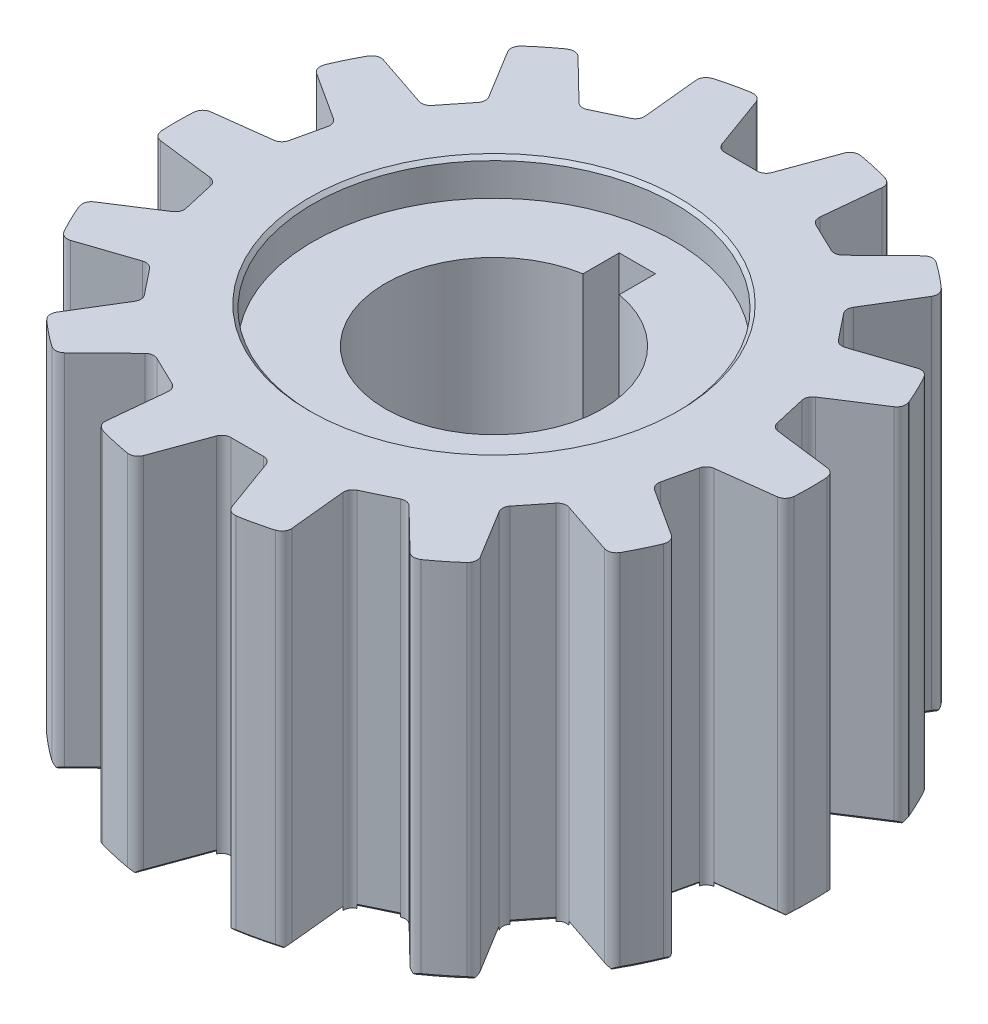
SolidWorks part; units mm, degrees
ref_plane "Alzado" through (0, 0, 0) normal (0, 0, 1) x (1, 0, 0)
ref_plane "Planta" through (0, 0, 0) normal (0, 1, 0) x (1, 0, 0)
ref_plane "Vista lateral" through (0, 0, 0) normal (1, 0, 0) x (0, 0, -1)
sketch "Croquis1" plane through (0, 0, 0) normal (0, 1, 0) x (1, 0, 0)
  circle A5 centre (0, 0) radius 6
  circle A8 centre (0, 0) radius 17.5
  dimension "D1" = 12
  dimension "D2" = 35
extrude "Saliente-Extruir1" add sketch "Croquis1" along normal blind 20
sketch "Croquis2" plane through (0, 20, 0) normal (0, 1, 0) x (1, 0, 0)
  line L0 (5.916, 12.2847) -> (7.0422, 11.7423)
  line L1 (7.0422, 11.7423) -> (9.8402, 14.4714)
  line L2 (0, 13.635) -> (-1.25, 13.635)
  line L3 (0, 13.635) -> (1.25, 13.635)
  line L4 (1.25, 13.635) -> (2.5868, 17.3078)
  line L6 (-2.5868, 17.3078) -> (-1.25, 13.635)
  line L7 (5.1789, 16.7161) -> (4.7898, 12.8271)
  line L8 (5.916, 12.2847) -> (4.7898, 12.8271)
  line L9 (10.6603, 8.5013) -> (11.4396, 7.524)
  line L10 (11.4396, 7.524) -> (15.1446, 8.7688)
  line L11 (11.9189, 12.8136) -> (9.8809, 9.4786)
  line L12 (10.6603, 8.5013) -> (9.8809, 9.4786)
  line L13 (13.2931, 3.0341) -> (13.5713, 1.8154)
  line L14 (13.5713, 1.8154) -> (17.4494, 1.3294)
  line L15 (16.2982, 6.3733) -> (13.015, 4.2527)
  line L16 (13.2931, 3.0341) -> (13.015, 4.2527)
  line L17 (13.2931, -3.0341) -> (13.015, -4.2527)
  line L18 (13.015, -4.2527) -> (16.2982, -6.3733)
  line L19 (17.4494, -1.3294) -> (13.5713, -1.8154)
  line L20 (13.2931, -3.0341) -> (13.5713, -1.8154)
  line L21 (10.6603, -8.5013) -> (9.8809, -9.4786)
  line L22 (9.8809, -9.4786) -> (11.9189, -12.8136)
  line L23 (15.1446, -8.7688) -> (11.4396, -7.524)
  line L24 (10.6603, -8.5013) -> (11.4396, -7.524)
  line L25 (5.916, -12.2847) -> (4.7898, -12.8271)
  line L26 (4.7898, -12.8271) -> (5.1789, -16.7161)
  line L27 (9.8402, -14.4714) -> (7.0422, -11.7423)
  line L28 (5.916, -12.2847) -> (7.0422, -11.7423)
  line L29 (0, -13.635) -> (-1.25, -13.635)
  line L30 (-1.25, -13.635) -> (-2.5868, -17.3078)
  line L31 (2.5868, -17.3078) -> (1.25, -13.635)
  line L32 (0, -13.635) -> (1.25, -13.635)
  line L33 (-5.916, -12.2847) -> (-7.0422, -11.7423)
  line L34 (-7.0422, -11.7423) -> (-9.8402, -14.4714)
  line L35 (-5.1789, -16.7161) -> (-4.7898, -12.8271)
  line L36 (-5.916, -12.2847) -> (-4.7898, -12.8271)
  line L37 (-10.6603, -8.5013) -> (-11.4396, -7.524)
  line L38 (-11.4396, -7.524) -> (-15.1446, -8.7688)
  line L39 (-11.9189, -12.8136) -> (-9.8809, -9.4786)
  line L40 (-10.6603, -8.5013) -> (-9.8809, -9.4786)
  line L41 (-13.2931, -3.0341) -> (-13.5713, -1.8154)
  line L42 (-13.5713, -1.8154) -> (-17.4494, -1.3294)
  line L43 (-16.2982, -6.3733) -> (-13.015, -4.2527)
  line L44 (-13.2931, -3.0341) -> (-13.015, -4.2527)
  line L45 (-13.2931, 3.0341) -> (-13.015, 4.2527)
  line L46 (-13.015, 4.2527) -> (-16.2982, 6.3733)
  line L47 (-17.4494, 1.3294) -> (-13.5713, 1.8154)
  line L48 (-13.2931, 3.0341) -> (-13.5713, 1.8154)
  line L49 (-10.6603, 8.5013) -> (-9.8809, 9.4786)
  line L50 (-9.8809, 9.4786) -> (-11.9189, 12.8136)
  line L51 (-15.1446, 8.7688) -> (-11.4396, 7.524)
  line L52 (-10.6603, 8.5013) -> (-11.4396, 7.524)
  line L53 (-5.916, 12.2847) -> (-4.7898, 12.8271)
  line L54 (-4.7898, 12.8271) -> (-5.1789, 16.7161)
  line L55 (-9.8402, 14.4714) -> (-7.0422, 11.7423)
  line L56 (-5.916, 12.2847) -> (-7.0422, 11.7423)
  circle A0 centre (0, 0) radius 17.5 construction
  arc A1 (-2.5868, 17.3078) -> (2.5868, 17.3078) centre (0, 0) cw
  arc A2 (5.1789, 16.7161) -> (9.8402, 14.4714) centre (0, 0) cw
  arc A3 (11.9189, 12.8136) -> (15.1446, 8.7688) centre (0, 0) cw
  arc A4 (16.2982, 6.3733) -> (17.4494, 1.3294) centre (0, 0) cw
  arc A5 (17.4494, -1.3294) -> (16.2982, -6.3733) centre (0, 0) cw
  arc A6 (15.1446, -8.7688) -> (11.9189, -12.8136) centre (0, 0) cw
  arc A7 (9.8402, -14.4714) -> (5.1789, -16.7161) centre (0, 0) cw
  arc A8 (2.5868, -17.3078) -> (-2.5868, -17.3078) centre (0, 0) cw
  arc A9 (-5.1789, -16.7161) -> (-9.8402, -14.4714) centre (0, 0) cw
  arc A10 (-11.9189, -12.8136) -> (-15.1446, -8.7688) centre (0, 0) cw
  arc A11 (-16.2982, -6.3733) -> (-17.4494, -1.3294) centre (0, 0) cw
  arc A12 (-17.4494, 1.3294) -> (-16.2982, 6.3733) centre (0, 0) cw
  arc A13 (-15.1446, 8.7688) -> (-11.9189, 12.8136) centre (0, 0) cw
  arc A14 (-9.8402, 14.4714) -> (-5.1789, 16.7161) centre (0, 0) cw
  dimension "D1" = 14
  dimension "D2" = 1.25
  dimension "D3" = 1.25
  dimension "D4" = 110
  dimension "D5" = 110
extrude "Cortar-Extruir2" cut sketch "Croquis2" against normal blind 20
sketch "Croquis3" plane through (0, 20, 0) normal (0, 1, 0) x (1, 0, 0)
  line L1 (-1, 5.9161) -> (-1, 7.9161)
  line L2 (-1, 7.9161) -> (1, 7.9161)
  line L3 (1, 7.9161) -> (1, 5.9161)
  circle A0 centre (0, 0) radius 6 construction
  arc A1 (1, 5.9161) -> (-1, 5.9161) centre (0, 0) ccw
  point P7 (0, 0)
  point P11 (0, 0)
  dimension "D1" = 2
  dimension "D2" = 2
extrude "Cortar-Extruir3" cut sketch "Croquis3" against normal blind 20
sketch "Croquis4" plane through (0, 20, 0) normal (0, 1, 0) x (1, 0, 0)
  circle A0 centre (0, 0) radius 10
  dimension "D1" = 20
extrude "Cortar-Extruir4" cut sketch "Croquis4" against normal blind 2
sketch "Croquis5" plane through (0, 0, 0) normal (0, -1, 0) x (1, 0, 0)
  circle A0 centre (0, 0) radius 10
  dimension "D1" = 20
extrude "Cortar-Extruir5" cut sketch "Croquis5" against normal blind 2
chamfer "Chaflán2" distance 0.2 angle 45 57 edges at (4.9844, 0, -14.7716) (3.8941, 0, -17.0612) (1.9184, 0, -15.4714) (0, 0, -13.635) (-1.9184, 0, -15.4714) (-3.8941, 0, -17.0612) (-4.9844, 0, -14.7716) (-5.916, 0, -12.2847) (-8.4412, 0, -13.1069) (-10.9111, 0, -13.6821) (-10.8999, 0, -11.1461) (-10.6603, 0, -8.5013) (-13.2921, 0, -8.1464) (-15.767, 0, -7.593) (-14.6566, 0, -5.313) (-13.2931, 0, -3.0341) (-15.5104, 0, -1.5724) (-17.5, 0, 0) (-15.5104, 0, 1.5724) (-13.2931, 0, 3.0341) (-14.6566, 0, 5.313) (-15.767, 0, 7.593) (-13.2921, 0, 8.1464) (-10.6603, 0, 8.5013) (-10.8999, 0, 11.1461) (-10.9111, 0, 13.6821) (-8.4412, 0, 13.1069) (-5.916, 0, 12.2847) (-4.9844, 0, 14.7716) (-3.8941, 0, 17.0612) (-1.9184, 0, 15.4714) (0, 0, 13.635) (1.9184, 0, 15.4714) (3.8941, 0, 17.0612) (4.9844, 0, 14.7716) (5.916, 0, 12.2847) (8.4412, 0, 13.1069) (10.9111, 0, 13.6821) (10.8999, 0, 11.1461) (10.6603, 0, 8.5013) (13.2921, 0, 8.1464) (15.767, 0, 7.593) (14.6566, 0, 5.313) (13.2931, 0, 3.0341) (15.5104, 0, 1.5724) (17.5, 0, 0) (15.5104, 0, -1.5724) (13.2931, 0, -3.0341) (14.6566, 0, -5.313) (15.767, 0, -7.593) (13.2921, 0, -8.1464) (10.6603, 0, -8.5013) (10.8999, 0, -11.1461) (10.9111, 0, -13.6821) (8.4412, 0, -13.1069) (5.916, 0, -12.2847) (0, 0, -10)
chamfer "Chaflán3" distance 0.2 angle 45 1 edges at (0, 20, 10)
sketch "Croquis6" plane through (0, 20, 0) normal (0, 1, 0) x (1, 0, 0)
  line L0 (-11.7715, 7.6355) -> (-11.4396, 7.524)
  line L1 (-11.4396, 7.524) -> (-11.2213, 7.7977)
  line L2 (-4.7898, 12.8271) -> (-4.8246, 13.1754)
  line L3 (-10.0992, 9.2048) -> (-9.8809, 9.4786)
  line L4 (-5.1052, 12.6752) -> (-4.7898, 12.8271)
  line L5 (-9.8809, 9.4786) -> (-10.0635, 9.7773)
  line L6 (-7.0422, 11.7423) -> (-6.7268, 11.8942)
  line L7 (-7.2928, 11.9868) -> (-7.0422, 11.7423)
  line L8 (1.25, 13.635) -> (1.3697, 13.964)
  line L9 (0.8999, 13.635) -> (1.25, 13.635)
  line L10 (-1.25, 13.635) -> (-0.8999, 13.635)
  line L11 (-1.3697, 13.964) -> (-1.25, 13.635)
  line L12 (7.0422, 11.7423) -> (7.2928, 11.9868)
  line L13 (6.7268, 11.8942) -> (7.0422, 11.7423)
  line L14 (4.7898, 12.8271) -> (5.1052, 12.6752)
  line L15 (4.8246, 13.1754) -> (4.7898, 12.8271)
  line L16 (11.4396, 7.524) -> (11.7715, 7.6355)
  line L17 (11.2213, 7.7977) -> (11.4396, 7.524)
  line L18 (9.8809, 9.4786) -> (10.0992, 9.2048)
  line L19 (10.0635, 9.7773) -> (9.8809, 9.4786)
  line L20 (13.5713, 1.8154) -> (13.9187, 1.7719)
  line L21 (13.4934, 2.1567) -> (13.5713, 1.8154)
  line L22 (13.015, 4.2527) -> (13.0929, 3.9114)
  line L23 (13.3091, 4.4427) -> (13.015, 4.2527)
  line L24 (13.015, -4.2527) -> (13.3091, -4.4427)
  line L25 (13.0929, -3.9114) -> (13.015, -4.2527)
  line L26 (13.5713, -1.8154) -> (13.4934, -2.1567)
  line L27 (13.9187, -1.7719) -> (13.5713, -1.8154)
  line L28 (9.8809, -9.4786) -> (10.0635, -9.7773)
  line L29 (10.0992, -9.2048) -> (9.8809, -9.4786)
  line L30 (11.4396, -7.524) -> (11.2213, -7.7977)
  line L31 (11.7715, -7.6355) -> (11.4396, -7.524)
  line L32 (4.7898, -12.8271) -> (4.8246, -13.1754)
  line L33 (5.1052, -12.6752) -> (4.7898, -12.8271)
  line L34 (7.0422, -11.7423) -> (6.7268, -11.8942)
  line L35 (7.2928, -11.9868) -> (7.0422, -11.7423)
  line L36 (-1.25, -13.635) -> (-1.3697, -13.964)
  line L37 (-0.8999, -13.635) -> (-1.25, -13.635)
  line L38 (1.25, -13.635) -> (0.8999, -13.635)
  line L39 (1.3697, -13.964) -> (1.25, -13.635)
  line L40 (-7.0422, -11.7423) -> (-7.2928, -11.9868)
  line L41 (-6.7268, -11.8942) -> (-7.0422, -11.7423)
  line L42 (-4.7898, -12.8271) -> (-5.1052, -12.6752)
  line L43 (-4.8246, -13.1754) -> (-4.7898, -12.8271)
  line L44 (-11.4396, -7.524) -> (-11.7715, -7.6355)
  line L45 (-11.2213, -7.7977) -> (-11.4396, -7.524)
  line L46 (-9.8809, -9.4786) -> (-10.0992, -9.2048)
  line L47 (-10.0635, -9.7773) -> (-9.8809, -9.4786)
  line L48 (-13.5713, -1.8154) -> (-13.9187, -1.7719)
  line L49 (-13.4934, -2.1567) -> (-13.5713, -1.8154)
  line L50 (-13.015, -4.2527) -> (-13.0929, -3.9114)
  line L51 (-13.3091, -4.4427) -> (-13.015, -4.2527)
  line L52 (-13.015, 4.2527) -> (-13.3091, 4.4427)
  line L53 (-13.0929, 3.9114) -> (-13.015, 4.2527)
  line L54 (-13.5713, 1.8154) -> (-13.4934, 2.1567)
  line L55 (-13.9187, 1.7719) -> (-13.5713, 1.8154)
  arc A0 (-10.0992, 9.2048) -> (-10.0635, 9.7773) centre (-10.4901, 9.5166) ccw
  arc A1 (-11.2213, 7.7977) -> (-11.7715, 7.6355) centre (-11.6123, 8.1095) cw
  arc A2 (-5.1052, 12.6752) -> (-4.8246, 13.1754) centre (-5.3222, 13.1256) ccw
  arc A3 (-6.7268, 11.8942) -> (-7.2928, 11.9868) centre (-6.9437, 12.3447) cw
  arc A4 (0.8999, 13.635) -> (1.3697, 13.964) centre (0.8999, 14.135) ccw
  arc A5 (-0.8999, 13.635) -> (-1.3697, 13.964) centre (-0.8999, 14.135) cw
  arc A6 (6.7268, 11.8942) -> (7.2928, 11.9868) centre (6.9437, 12.3447) ccw
  arc A7 (5.1052, 12.6752) -> (4.8246, 13.1754) centre (5.3222, 13.1256) cw
  arc A8 (11.2213, 7.7977) -> (11.7715, 7.6355) centre (11.6123, 8.1095) ccw
  arc A9 (10.0992, 9.2048) -> (10.0635, 9.7773) centre (10.4901, 9.5166) cw
  arc A10 (13.4934, 2.1567) -> (13.9187, 1.7719) centre (13.9808, 2.268) ccw
  arc A11 (13.0929, 3.9114) -> (13.3091, 4.4427) centre (13.5803, 4.0227) cw
  arc A12 (13.0929, -3.9114) -> (13.3091, -4.4427) centre (13.5803, -4.0227) ccw
  arc A13 (13.4934, -2.1567) -> (13.9187, -1.7719) centre (13.9808, -2.268) cw
  arc A14 (10.0992, -9.2048) -> (10.0635, -9.7773) centre (10.4901, -9.5166) ccw
  arc A15 (11.2213, -7.7977) -> (11.7715, -7.6355) centre (11.6123, -8.1095) cw
  arc A16 (5.1052, -12.6752) -> (4.8246, -13.1754) centre (5.3222, -13.1256) ccw
  arc A17 (6.7268, -11.8942) -> (7.2928, -11.9868) centre (6.9437, -12.3447) cw
  arc A18 (-0.8999, -13.635) -> (-1.3697, -13.964) centre (-0.8999, -14.135) ccw
  arc A19 (0.8999, -13.635) -> (1.3697, -13.964) centre (0.8999, -14.135) cw
  arc A20 (-6.7268, -11.8942) -> (-7.2928, -11.9868) centre (-6.9437, -12.3447) ccw
  arc A21 (-5.1052, -12.6752) -> (-4.8246, -13.1754) centre (-5.3222, -13.1256) cw
  arc A22 (-11.2213, -7.7977) -> (-11.7715, -7.6355) centre (-11.6123, -8.1095) ccw
  arc A23 (-10.0992, -9.2048) -> (-10.0635, -9.7773) centre (-10.4901, -9.5166) cw
  arc A24 (-13.4934, -2.1567) -> (-13.9187, -1.7719) centre (-13.9808, -2.268) ccw
  arc A25 (-13.0929, -3.9114) -> (-13.3091, -4.4427) centre (-13.5803, -4.0227) cw
  arc A26 (-13.0929, 3.9114) -> (-13.3091, 4.4427) centre (-13.5803, 4.0227) ccw
  arc A27 (-13.4934, 2.1567) -> (-13.9187, 1.7719) centre (-13.9808, 2.268) cw
  point P13 (-9.8809, 9.4786)
  point P16 (-11.4396, 7.524)
  dimension "D1" = 0.5
  dimension "D2" = 0.5
  dimension "D3" = 14
extrude "Saliente-Extruir3" add sketch "Croquis6" against normal blind 20
sketch "Croquis8" plane through (0, 20, 0) normal (0, 1, 0) x (1, 0, 0)
  line L0 (-11.6975, 12.4513) -> (-11.9189, 12.8136)
  line L1 (-11.9189, 12.8136) -> (-12.159, 13.2065)
  line L4 (-12.159, 13.2065) -> (-11.7581, 13.4515)
  line L5 (-11.7581, 13.4515) -> (-11.5972, 13.0908)
  line L6 (-10.1116, 14.7496) -> (-10.3273, 14.4714)
  line L7 (-10.3273, 14.4714) -> (-10.182, 14.2195)
  line L8 (-9.8402, 14.4714) -> (-9.5362, 14.1749)
  line L9 (-5.1367, 16.2936) -> (-5.1789, 16.7161)
  line L10 (-5.1789, 16.7161) -> (-5.2248, 17.1742)
  line L11 (-5.2248, 17.1742) -> (-4.7573, 17.221)
  line L12 (-4.7573, 17.221) -> (-4.7689, 16.8263)
  line L13 (-2.5868, 17.3078) -> (-2.4416, 16.9087)
  line L14 (-3.0257, 17.5191) -> (-3.004, 17.2291)
  line L15 (-2.7106, 17.6761) -> (-3.0257, 17.5191)
  line L16 (2.4416, 16.9087) -> (2.5868, 17.3078)
  line L17 (2.5868, 17.3078) -> (2.7442, 17.7404)
  line L18 (2.7442, 17.7404) -> (3.1858, 17.5797)
  line L19 (3.1858, 17.5797) -> (3.004, 17.2291)
  line L20 (5.1789, 16.7161) -> (5.1367, 16.2936)
  line L21 (4.8752, 17.097) -> (4.7689, 16.8263)
  line L22 (5.2272, 17.1017) -> (4.8752, 17.097)
  line L23 (9.5362, 14.1749) -> (9.8402, 14.4714)
  line L24 (9.8402, 14.4714) -> (10.1697, 14.7929)
  line L25 (10.1697, 14.7929) -> (10.4978, 14.4565)
  line L26 (10.4978, 14.4565) -> (10.182, 14.2195)
  line L27 (11.9189, 12.8136) -> (11.6975, 12.4513)
  line L28 (11.8105, 13.2886) -> (11.5972, 13.0908)
  line L29 (12.1297, 13.1401) -> (11.8105, 13.2886)
  line L30 (14.7421, 8.6335) -> (15.1446, 8.7688)
  line L31 (15.1446, 8.7688) -> (15.581, 8.9154)
  line L32 (15.581, 8.9154) -> (15.7306, 8.47)
  line L33 (15.7306, 8.47) -> (15.3432, 8.3935)
  line L34 (16.2982, 6.3733) -> (15.9415, 6.1429)
  line L35 (16.4066, 6.8482) -> (16.1286, 6.7626)
  line L36 (16.6298, 6.576) -> (16.4066, 6.8482)
  line L37 (17.0281, 1.3822) -> (17.4494, 1.3294)
  line L38 (17.4494, 1.3294) -> (17.9063, 1.2722)
  line L39 (17.9063, 1.2722) -> (17.8478, 0.806)
  line L40 (17.8478, 0.806) -> (17.4656, 0.9051)
  line L41 (17.4494, -1.3294) -> (17.0281, -1.3822)
  line L42 (17.7532, -0.9485) -> (17.4656, -0.9051)
  line L43 (17.8361, -1.2906) -> (17.7532, -0.9485)
  line L44 (15.9415, -6.1429) -> (16.2982, -6.3733)
  line L45 (16.2982, -6.3733) -> (16.685, -6.6231)
  line L46 (16.685, -6.6231) -> (16.43, -7.0177)
  line L47 (16.43, -7.0177) -> (16.1286, -6.7626)
  line L48 (15.1446, -8.7688) -> (14.7421, -8.6335)
  line L49 (15.5835, -8.5574) -> (15.3432, -8.3935)
  line L50 (15.5098, -8.9016) -> (15.5835, -8.5574)
  line L51 (11.6975, -12.4513) -> (11.9189, -12.8136)
  line L52 (11.9189, -12.8136) -> (12.159, -13.2065)
  line L53 (12.159, -13.2065) -> (11.7581, -13.4515)
  line L54 (11.7581, -13.4515) -> (11.5972, -13.0908)
  line L55 (9.8402, -14.4714) -> (9.5362, -14.1749)
  line L56 (10.3273, -14.4714) -> (10.182, -14.2195)
  line L57 (10.1116, -14.7496) -> (10.3273, -14.4714)
  line L58 (5.1367, -16.2936) -> (5.1789, -16.7161)
  line L59 (5.1789, -16.7161) -> (5.2248, -17.1742)
  line L60 (5.2248, -17.1742) -> (4.7573, -17.221)
  line L61 (4.7573, -17.221) -> (4.7689, -16.8263)
  line L62 (2.5868, -17.3078) -> (2.4416, -16.9087)
  line L63 (3.0257, -17.5191) -> (3.004, -17.2291)
  line L64 (2.7106, -17.6761) -> (3.0257, -17.5191)
  line L65 (-2.4416, -16.9087) -> (-2.5868, -17.3078)
  line L66 (-2.5868, -17.3078) -> (-2.7442, -17.7404)
  line L67 (-2.7442, -17.7404) -> (-3.1858, -17.5797)
  line L68 (-3.1858, -17.5797) -> (-3.004, -17.2291)
  line L69 (-5.1789, -16.7161) -> (-5.1367, -16.2936)
  line L70 (-4.8752, -17.097) -> (-4.7689, -16.8263)
  line L71 (-5.2272, -17.1017) -> (-4.8752, -17.097)
  line L72 (-9.5362, -14.1749) -> (-9.8402, -14.4714)
  line L73 (-9.8402, -14.4714) -> (-10.1697, -14.7929)
  line L74 (-10.1697, -14.7929) -> (-10.4978, -14.4565)
  line L75 (-10.4978, -14.4565) -> (-10.182, -14.2195)
  line L76 (-11.9189, -12.8136) -> (-11.6975, -12.4513)
  line L77 (-11.8105, -13.2886) -> (-11.5972, -13.0908)
  line L78 (-12.1297, -13.1401) -> (-11.8105, -13.2886)
  line L79 (-14.7421, -8.6335) -> (-15.1446, -8.7688)
  line L80 (-15.1446, -8.7688) -> (-15.581, -8.9154)
  line L81 (-15.581, -8.9154) -> (-15.7306, -8.47)
  line L82 (-15.7306, -8.47) -> (-15.3432, -8.3935)
  line L83 (-16.2982, -6.3733) -> (-15.9415, -6.1429)
  line L84 (-16.4066, -6.8482) -> (-16.1286, -6.7626)
  line L85 (-16.6298, -6.576) -> (-16.4066, -6.8482)
  line L86 (-17.0281, -1.3822) -> (-17.4494, -1.3294)
  line L87 (-17.4494, -1.3294) -> (-17.9063, -1.2722)
  line L88 (-17.9063, -1.2722) -> (-17.8478, -0.806)
  line L89 (-17.8478, -0.806) -> (-17.4656, -0.9051)
  line L90 (-17.4494, 1.3294) -> (-17.0281, 1.3822)
  line L91 (-17.7532, 0.9485) -> (-17.4656, 0.9051)
  line L92 (-17.8361, 1.2906) -> (-17.7532, 0.9485)
  line L93 (-15.9415, 6.1429) -> (-16.2982, 6.3733)
  line L94 (-16.2982, 6.3733) -> (-16.685, 6.6231)
  line L95 (-16.685, 6.6231) -> (-16.43, 7.0177)
  line L96 (-16.43, 7.0177) -> (-16.1286, 6.7626)
  line L97 (-15.1446, 8.7688) -> (-14.7421, 8.6335)
  line L98 (-15.5835, 8.5574) -> (-15.3432, 8.3935)
  line L99 (-15.5098, 8.9016) -> (-15.5835, 8.5574)
  arc A0 (-9.8402, 14.4714) -> (-10.1116, 14.7496) centre (-10.9777, 13.6329) ccw
  arc A1 (-11.6975, 12.4513) -> (-11.5972, 13.0908) centre (-11.2709, 12.712) cw
  arc A2 (-9.5362, 14.1749) -> (-10.182, 14.2195) centre (-9.8853, 13.817) ccw
  arc A3 (-5.1367, 16.2936) -> (-4.7689, 16.8263) centre (-4.6392, 16.3434) cw
  arc A4 (-2.4416, 16.9087) -> (-3.004, 17.2291) centre (-2.9114, 16.7377) ccw
  arc A5 (-2.5868, 17.3078) -> (-2.7106, 17.6761) centre (-3.9755, 17.0459) ccw
  arc A6 (2.4416, 16.9087) -> (3.004, 17.2291) centre (2.9114, 16.7377) cw
  arc A7 (5.1367, 16.2936) -> (4.7689, 16.8263) centre (4.6392, 16.3434) ccw
  arc A8 (5.1789, 16.7161) -> (5.2272, 17.1017) centre (3.8142, 17.0827) ccw
  arc A9 (9.5362, 14.1749) -> (10.182, 14.2195) centre (9.8853, 13.817) cw
  arc A10 (11.6975, 12.4513) -> (11.5972, 13.0908) centre (11.2709, 12.712) ccw
  arc A11 (11.9189, 12.8136) -> (12.1297, 13.1401) centre (10.8484, 13.7361) ccw
  arc A12 (14.7421, 8.6335) -> (15.3432, 8.3935) centre (14.9013, 8.1596) cw
  arc A13 (15.9415, 6.1429) -> (16.1286, 6.7626) centre (15.6702, 6.5629) ccw
  arc A14 (16.2982, 6.3733) -> (16.6298, 6.576) centre (15.7339, 7.6689) ccw
  arc A15 (17.0281, 1.3822) -> (17.4656, 0.9051) centre (16.9659, 0.8861) cw
  arc A16 (17.0281, -1.3822) -> (17.4656, -0.9051) centre (16.9659, -0.8861) ccw
  arc A17 (17.4494, -1.3294) -> (17.8361, -1.2906) centre (17.5031, 0.0827) ccw
  arc A18 (15.9415, -6.1429) -> (16.1286, -6.7626) centre (15.6702, -6.5629) cw
  arc A19 (14.7421, -8.6335) -> (15.3432, -8.3935) centre (14.9013, -8.1596) ccw
  arc A20 (15.1446, -8.7688) -> (15.5098, -8.9016) centre (15.8057, -7.5198) ccw
  arc A21 (11.6975, -12.4513) -> (11.5972, -13.0908) centre (11.2709, -12.712) cw
  arc A22 (9.5362, -14.1749) -> (10.182, -14.2195) centre (9.8853, -13.817) ccw
  arc A23 (9.8402, -14.4714) -> (10.1116, -14.7496) centre (10.9777, -13.6329) ccw
  arc A24 (5.1367, -16.2936) -> (4.7689, -16.8263) centre (4.6392, -16.3434) cw
  arc A25 (2.4416, -16.9087) -> (3.004, -17.2291) centre (2.9114, -16.7377) ccw
  arc A26 (2.5868, -17.3078) -> (2.7106, -17.6761) centre (3.9755, -17.0459) ccw
  arc A27 (-2.4416, -16.9087) -> (-3.004, -17.2291) centre (-2.9114, -16.7377) cw
  arc A28 (-5.1367, -16.2936) -> (-4.7689, -16.8263) centre (-4.6392, -16.3434) ccw
  arc A29 (-5.1789, -16.7161) -> (-5.2272, -17.1017) centre (-3.8142, -17.0827) ccw
  arc A30 (-9.5362, -14.1749) -> (-10.182, -14.2195) centre (-9.8853, -13.817) cw
  arc A31 (-11.6975, -12.4513) -> (-11.5972, -13.0908) centre (-11.2709, -12.712) ccw
  arc A32 (-11.9189, -12.8136) -> (-12.1297, -13.1401) centre (-10.8484, -13.7361) ccw
  arc A33 (-14.7421, -8.6335) -> (-15.3432, -8.3935) centre (-14.9013, -8.1596) cw
  arc A34 (-15.9415, -6.1429) -> (-16.1286, -6.7626) centre (-15.6702, -6.5629) ccw
  arc A35 (-16.2982, -6.3733) -> (-16.6298, -6.576) centre (-15.7339, -7.6689) ccw
  arc A36 (-17.0281, -1.3822) -> (-17.4656, -0.9051) centre (-16.9659, -0.8861) cw
  arc A37 (-17.0281, 1.3822) -> (-17.4656, 0.9051) centre (-16.9659, 0.8861) ccw
  arc A38 (-17.4494, 1.3294) -> (-17.8361, 1.2906) centre (-17.5031, -0.0827) ccw
  arc A39 (-15.9415, 6.1429) -> (-16.1286, 6.7626) centre (-15.6702, 6.5629) cw
  arc A40 (-14.7421, 8.6335) -> (-15.3432, 8.3935) centre (-14.9013, 8.1596) ccw
  arc A41 (-15.1446, 8.7688) -> (-15.5098, 8.9016) centre (-15.8057, 7.5198) ccw
  point P16 (-11.9189, 12.8136)
  point P19 (-9.8402, 14.4714)
  dimension "D1" = 0.5
  dimension "D2" = 0.5
  dimension "D3" = 14
extrude "Cortar-Extruir9" cut sketch "Croquis8" against normal blind 20
